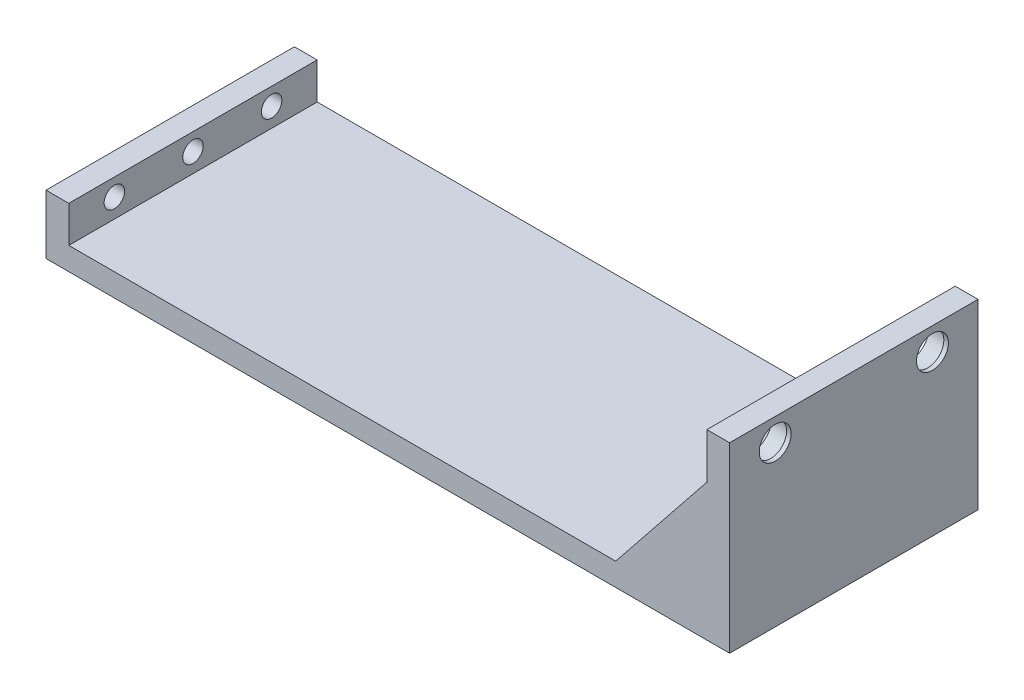
SolidWorks part; units mm, degrees
ref_plane "Front Plane" through (0, 0, 0) normal (0, 0, 1) x (1, 0, 0)
ref_plane "Top Plane" through (0, 0, 0) normal (0, 1, 0) x (1, 0, 0)
ref_plane "Right Plane" through (0, 0, 0) normal (1, 0, 0) x (0, 0, -1)
sketch "Sketch1" plane through (0, 0, 0) normal (0, 1, 0) x (1, 0, 0)
  line L2 (56.8875, -28.9394) -> (-93.1125, -28.9394)
  line L3 (56.8875, -28.9394) -> (56.8875, 25.5606)
  line L4 (56.8875, 25.5606) -> (-93.1125, 25.5606)
  line L5 (-93.1125, -28.9394) -> (-93.1125, 25.5606)
  dimension "D1" = 150
  dimension "D2" = 54.5
extrude "Boss-Extrude1" add sketch "Sketch1" along normal blind 5
sketch "Sketch2" plane through (0, 5, 0) normal (0, 1, 0) x (1, 0, 0)
  line L0 (-93.1125, -28.9394) -> (56.8875, -28.9394) construction
  line L1 (-93.1125, 25.5606) -> (-88.1125, 25.5606)
  line L2 (-93.1125, 25.5606) -> (-93.1125, -28.9394)
  line L3 (-93.1125, -28.9394) -> (-88.1125, -28.9394)
  line L4 (-88.1125, 25.5606) -> (-88.1125, -28.9394)
  dimension "D1" = 5
extrude "Boss-Extrude2" add sketch "Sketch2" along normal blind 8
hole_wizard "#8 Clearance Hole1" positions "3DSketch1" profile "Sketch3" hole size "#8" standard "ANSI Inch"
sketch3d "3DSketch1"
  line L1 (-93.1125, 13, -25.5606) -> (-93.1125, 13, 28.9394) construction
  line L2 (-93.1125, 13, -25.5606) -> (-93.1125, 0, -25.5606) construction
  line L3 (-93.1125, 13, 28.9394) -> (-93.1125, 0, 28.9394) construction
  point P0 (-93.1125, 9.2, -15.5606)
  point P2 (-93.1125, 9.2, 1.6894)
  point P4 (-93.1125, 9.2, 18.9394)
  dimension "D1" = 3.8
  dimension "D2" = 3.8
  dimension "D3" = 3.8
  dimension "D4" = 10
  dimension "D5" = 27.25
  dimension "D6" = 10
sketch "Sketch3" plane through (-93.1125, 9.2, -15.5606) normal (0, 1, 0) x (0, 0, 1)
  line L0 (0, 0) -> (0, 18.3507)
  line L1 (0, 18.3507) -> (2.2479, 17)
  line L2 (2.2479, 17) -> (2.2479, 0)
  line L5 (2.2479, 0) -> (0, 0)
  line L10 (0, 18.3507) -> (-2.2479, 17) construction
  line L11 (0, -6.35) -> (0, 107.95) construction
  dimension "Hole Dia." = 4.4958
  dimension "Hole Depth" = 17
  dimension "Drill Angle" = 118
sketch "Sketch7" plane through (0, 5, 0) normal (0, 1, 0) x (1, 0, 0)
  line L0 (56.8875, 25.5606) -> (-88.1125, 25.5606) construction
  line L1 (56.8875, -28.9394) -> (51.8875, -28.9394)
  line L2 (56.8875, -28.9394) -> (56.8875, 25.5606)
  line L3 (56.8875, 25.5606) -> (51.8875, 25.5606)
  line L4 (51.8875, -28.9394) -> (51.8875, 25.5606)
  dimension "D1" = 5
extrude "Boss-Extrude3" add sketch "Sketch7" along normal blind 35
sketch "Sketch8" plane through (51.8875, 0, 0) normal (-1, 0, 0) x (0, 0, 1)
  line L0 (-25.5606, 40) -> (28.9394, 40) construction
  line L1 (-25.5606, 40) -> (-25.5606, 5) construction
  line L2 (28.9394, 40) -> (28.9394, 5) construction
  circle A0 centre (-15.5606, 35) radius 4.25
  circle A1 centre (18.9394, 35) radius 4.25
  dimension "D1" = 8.5
  dimension "D2" = 8.5
  dimension "D3" = 5
  dimension "D4" = 5
  dimension "D5" = 10
  dimension "D6" = 10
extrude "Cut-Extrude1" cut sketch "Sketch8" against normal blind 4
sketch "Sketch10" plane through (0, 0, -25.5606) normal (0, 0, -1) x (-1, 0, 0)
  line L0 (-51.8875, 30) -> (-31.8875, 5)
  line L1 (-51.8875, 40) -> (-51.8875, 5) construction
  line L2 (-51.8875, 5) -> (88.1125, 5) construction
  dimension "D1" = 10
  dimension "D2" = 20
rib "Rib1" sketch "Sketch10" sketch "Sketch10" thickness 10 extrusion direction parallel to sketch draft on no parameters "D1"=10
sketch "Sketch12" plane through (0, 0, 28.9394) normal (0, 0, 1) x (1, 0, 0)
  line L0 (51.8875, 30) -> (31.8875, 5)
  line L1 (51.8875, 40) -> (51.8875, 5) construction
  line L2 (-88.1125, 5) -> (51.8875, 5) construction
  dimension "D1" = 10
  dimension "D2" = 20
rib "Rib3" sketch "Sketch12" sketch "Sketch12" thickness 10 extrusion direction parallel to sketch draft on no parameters "D1"=10
sketch "Sketch13" plane through (51.8875, 0, 0) normal (-1, 0, 0) x (0, 0, 1)
  line L0 (-25.5606, 40) -> (28.9394, 40) construction
  line L1 (-2.3106, 30) -> (5.6894, 30)
  line L2 (-2.3106, 30) -> (-2.3106, 28)
  line L3 (-2.3106, 28) -> (5.6894, 28)
  line L4 (5.6894, 30) -> (5.6894, 28)
  line L5 (-25.5606, 40) -> (-25.5606, 30) construction
  line L6 (28.9394, 40) -> (28.9394, 30) construction
  dimension "D1" = 8
  dimension "D2" = 10
  dimension "D3" = 23.25
  dimension "D4" = 23.25
  dimension "D5" = 2
extrude "Boss-Extrude4" add sketch "Sketch13" along normal blind 5
sketch "Sketch14" plane through (0, 30, 0) normal (0, 1, 0) x (1, 0, 0)
  line L0 (46.8875, -5.6894) -> (46.8875, 2.3106) construction
  line L1 (46.8875, 2.3106) -> (51.8875, 2.3106) construction
  circle A0 centre (49.3875, -1.6894) radius 2
  dimension "D1" = 2.5
  dimension "D2" = 4
extrude "Cut-Extrude2" cut sketch "Sketch14" against normal blind 2
sketch "Sketch15" plane through (55.8875, 0, 0) normal (-1, 0, 0) x (0, 0, 1)
  circle A0 centre (-15.5606, 35) radius 3.5
  circle A1 centre (18.9394, 35) radius 3.5
extrude "Cut-Extrude3" cut sketch "Sketch15" against normal blind 1
